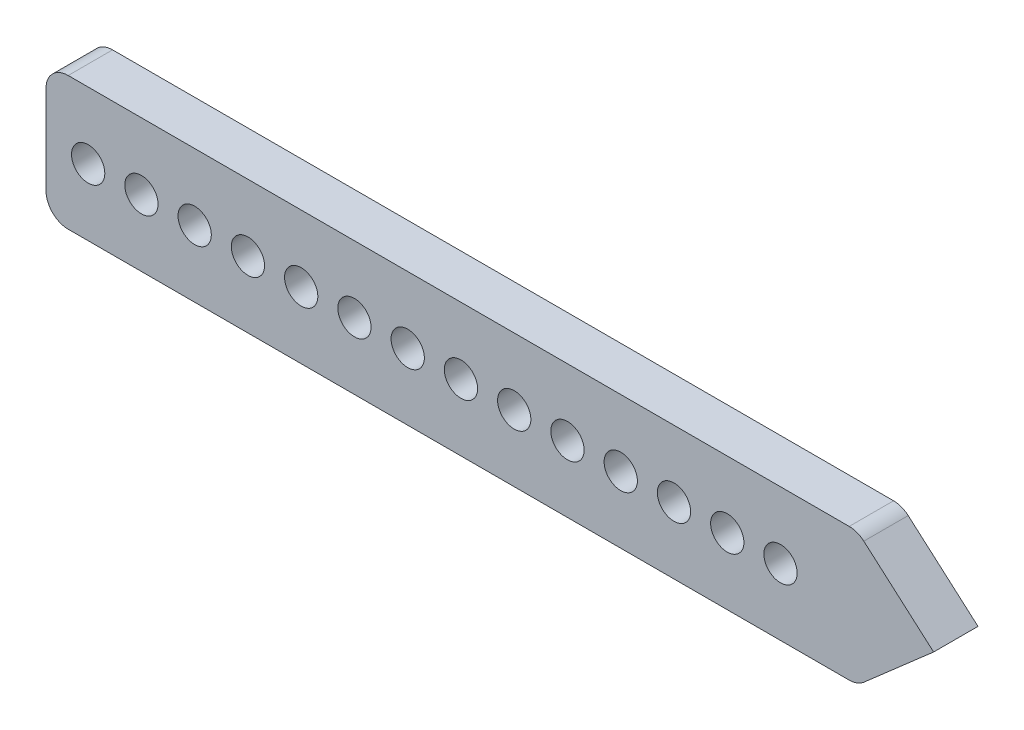
SolidWorks part; units mm, degrees
ref_plane "Front Plane" through (0, 0, 0) normal (0, 0, 1) x (1, 0, 0)
ref_plane "Top Plane" through (0, 0, 0) normal (0, 1, 0) x (1, 0, 0)
ref_plane "Right Plane" through (0, 0, 0) normal (1, 0, 0) x (0, 0, -1)
sketch "Croquis2" plane through (0, 0, 0) normal (0, 0, 1) x (1, 0, 0)
  line L0 (18.5685, -2.7526) -> (21.7143, 0)
  line L1 (-17.2857, 3) -> (17.91, 3)
  line L2 (-18.2857, 2) -> (-18.2857, -2)
  line L3 (-17.2857, -3) -> (17.91, -3)
  line L5 (-18.2857, 3) -> (18.2857, -3) construction
  line L6 (-18.2857, -3) -> (18.2857, 3) construction
  line L7 (21.7143, 0) -> (18.5685, 2.7526)
  circle A0 centre (-16.3857, 0) radius 0.75
  circle A1 centre (-13.9857, 0) radius 0.75
  circle A2 centre (-11.5857, 0) radius 0.75
  circle A3 centre (-9.1857, 0) radius 0.75
  arc A4 (17.91, -3) -> (18.5685, -2.7526) centre (17.91, -2) ccw
  arc A5 (17.91, 3) -> (18.5685, 2.7526) centre (17.91, 2) cw
  arc A6 (-18.2857, -2) -> (-17.2857, -3) centre (-17.2857, -2) ccw
  arc A7 (-17.2857, 3) -> (-18.2857, 2) centre (-17.2857, 2) ccw
  circle A8 centre (-6.7857, 0) radius 0.75
  circle A9 centre (-4.3857, 0) radius 0.75
  circle A10 centre (-1.9857, 0) radius 0.75
  circle A11 centre (0.4143, 0) radius 0.75
  circle A12 centre (2.8143, 0) radius 0.75
  circle A13 centre (5.2143, 0) radius 0.75
  circle A14 centre (7.6143, 0) radius 0.75
  circle A15 centre (10.0143, 0) radius 0.75
  circle A16 centre (12.4143, 0) radius 0.75
  circle A17 centre (14.8143, 0) radius 0.75
  point P0 (0, 0)
  dimension "D4" = 1.5
  dimension "D9" = 1
  dimension "D1" = 40
  dimension "D2" = 6
  dimension "D3" = 1.9
  dimension "D6" = 35.1957
  dimension "D7" = 35.1957
  dimension "D8" = 277.628
  dimension "D5" = 4
  dimension "D10" = 11
extrude "Saliente-Extruir1" add sketch "Croquis2" along normal blind 2
